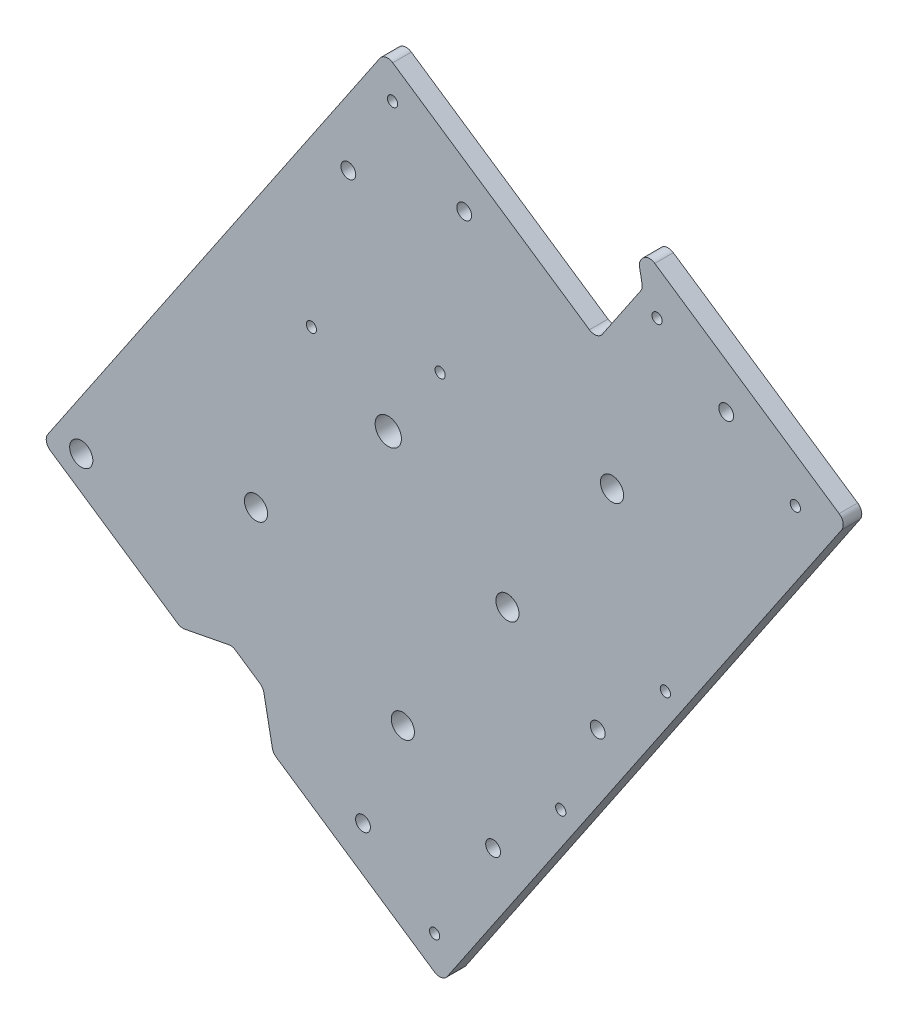
SolidWorks part; units mm, degrees
ref_plane "Front Plane" through (0, 0, 0) normal (0, 0, 1) x (1, 0, 0)
ref_plane "Top Plane" through (0, 0, 0) normal (0, 1, 0) x (1, 0, 0)
ref_plane "Right Plane" through (0, 0, 0) normal (1, 0, 0) x (0, 0, -1)
sketch "Sketch1" plane through (0, 0, 0) normal (0, 0, 1) x (1, 0, 0)
  line L0 (0, 31.75) -> (0, 57.15) construction
  line L1 (31.75, 0) -> (67.31, 0) construction
  line L3 (0, -31.75) -> (0, -97.79) construction
  line L4 (22.4506, -22.4506) -> (58.3717, -58.3717) construction
  line L5 (-22.4506, -22.4506) -> (-72.7401, -72.7401) construction
  line L6 (57.493, 23.8144) -> (29.3332, 12.1502) construction
  line L7 (-40.4112, 40.4112) -> (-22.4506, 22.4506) construction
  line L8 (42.2072, 42.2072) -> (22.4506, 22.4506) construction
  line L9 (71.5729, -29.6465) -> (29.3332, -12.1502) construction
  line L10 (33.5345, -80.9596) -> (12.1502, -29.3332) construction
  line L11 (-37.4226, -90.3462) -> (-12.1502, -29.3332) construction
  circle A0 centre (0, 0) radius 31.75 construction
  circle A3 centre (0, 0) radius 50.8 construction
  dimension "D4" = 63.5
  dimension "D24" = 101.6
  dimension "D2" = 25.4
  dimension "D3" = 35.56
  dimension "D5" = 66.04
  dimension "D6" = 45
  dimension "D7" = 50.8
  dimension "D8" = 71.12
  dimension "D9" = 45
  dimension "D10" = 45
  dimension "D11" = 27.94
  dimension "D12" = 45
  dimension "D13" = 22.5
  dimension "D14" = 22.5
  dimension "D15" = 22.5
  dimension "D16" = 25.4
  dimension "D17" = 45.72
  dimension "D18" = 55.88
  dimension "D19" = 66.04
  dimension "D20" = 22.5
  dimension "D21" = 30.48
sketch "Sketch6" plane through (0, 0, 0) normal (0, 0, 1) x (1, 0, 0)
  line L0 (0, 0) -> (0, 57.15) construction
  line L1 (-68.0069, -76.6709) -> (-109.4868, -48.6565)
  line L2 (-109.4868, -48.6565) -> (-73.9468, 3.9663) construction
  line L3 (-73.9468, 3.9663) -> (-56.6244, -7.7327)
  line L4 (-73.9468, 3.9663) -> (-1.0899, 111.8431)
  line L5 (-1.0899, 111.8431) -> (135.7295, 19.4391)
  line L6 (135.7295, 19.4391) -> (18.4476, -154.2162)
  line L7 (18.4476, -154.2162) -> (-118.3718, -61.8122)
  line L8 (-118.3718, -61.8122) -> (-109.4868, -48.6565)
  arc A0 (0, 57.15) -> (-56.6244, -7.7327) centre (0, 0) ccw
  arc A1 (0, 57.15) -> (70.8293, -29.3385) centre (1.3636, -13.9802) cw
  spline S0 degree 4 poles (72.5802, -14.4204) (72.5732, -14.8939) (72.5509, -15.8408) (72.5026, -17.0238) (72.4142, -18.4418) (72.3202, -19.622) (72.2329, -20.5651) (72.1094, -21.7358) (71.9666, -22.9009) (71.8046, -24.0602) (71.6239, -25.2132) (71.4679, -26.1331) (71.3203, -26.9417) (71.191, -27.6137) (71.0723, -28.2005) (70.9682, -28.6984) (70.8717, -29.1472) (70.8012, -29.4669) (70.7133, -29.8548) (70.619, -30.2629) (70.5011, -30.7621) (70.364, -31.3222) (70.1993, -31.971) (70.0005, -32.7239) (69.7951, -33.4698) (69.582, -34.2143) (69.3614, -34.9567) (69.1333, -35.6968) (68.8388, -36.6189) (68.4706, -37.7207) (68.0195, -38.9988) (67.4748, -40.4488) (66.9013, -41.8877) (66.2993, -43.3149) (65.6691, -44.7298) (65.0111, -46.132) (64.3256, -47.521) (63.613, -48.8963) (62.8736, -50.2574) (62.1078, -51.6038) (61.3159, -52.935) (60.4985, -54.2507) (59.6557, -55.5503) (58.5712, -57.1543) (57.221, -59.0453) (55.576, -61.2004) (53.604, -63.5903) (51.5433, -65.9041) (49.3973, -68.139) (47.1695, -70.2924) (44.8635, -72.3618) (42.4828, -74.3448) (40.0312, -76.2394) (36.8825, -78.4946) (32.9768, -81.016) (28.2508, -83.6809) (21.4155, -86.9191) (14.3083, -89.5267) (6.997, -91.4882) (-0.4519, -92.7974) (-6.6169, -93.4564) (-12.812, -93.702) (-19.0096, -93.5373) (-25.1831, -92.9667) (-31.3064, -91.9964) (-36.5985, -90.8043) (-41.0725, -89.5432) (-44.7523, -88.3359) (-47.6642, -87.2776) (-50.5413, -86.1284) (-53.3811, -84.8896) (-56.1809, -83.563) (-58.5935, -82.3267) (-60.6334, -81.2142) (-62.3138, -80.2525) (-63.6461, -79.4625) (-64.9661, -78.6522) (-66.2736, -77.8217) (-67.4063, -77.0777) (-68.3692, -76.4276) (-69.1659, -75.8779) (-69.7996, -75.4335) (-70.4313, -74.9832) (-71.06, -74.5278) (-71.6725, -74.0775) (-72.2987, -73.6093) (-72.9683, -73.0996) (-73.347, -72.808) (-73.9663, -72.325) (-74.6801, -71.7609) (-75.4046, -71.175) (-76.2838, -70.4507) (-77.1319, -69.735) (-77.9818, -69.0025) (-78.8195, -68.2643) (-79.6511, -67.5155) (-80.4737, -66.7585) (-81.4921, -65.8008) (-82.6974, -64.6343) (-83.8818, -63.4463) (-85.0447, -62.2374) (-85.8084, -61.4205) (-86.1873, -61.0093) (-86.376, -60.8031) knots 0 0 0 0 0 0.008941 0.017882 0.022352 0.026823 0.031293 0.035764 0.044578 0.048985 0.053392 0.057799 0.062207 0.06441 0.066614 0.068817 0.071021 0.072848 0.074676 0.076504 0.078332 0.081987 0.085642 0.089298 0.092953 0.096609 0.100264 0.103919 0.107575 0.114886 0.122197 0.129507 0.136818 0.144129 0.15144 0.158751 0.166062 0.173372 0.180683 0.187994 0.195305 0.202616 0.209927 0.217237 0.231859 0.246481 0.261102 0.275724 0.290346 0.304967 0.319589 0.334211 0.348832 0.363454 0.392697 0.421941 0.451184 0.506141 0.535384 0.564627 0.593871 0.623114 0.652357 0.681601 0.710844 0.740087 0.754709 0.769331 0.783952 0.798574 0.813196 0.827817 0.842439 0.84975 0.857061 0.864371 0.871682 0.878993 0.886304 0.889959 0.893615 0.89727 0.900926 0.904581 0.908237 0.911892 0.915547 0.918186 0.920826 0.926104 0.931382 0.936661 0.941939 0.947217 0.952495 0.957774 0.963052 0.96833 0.978887 0.989443 0.994722 1 1 1 1 1 construction
  spline S1 degree 4 poles (70.8293, -29.3385) (70.8117, -29.4183) (70.776, -29.5781) (70.7133, -29.8548) (70.619, -30.2629) (70.5011, -30.7621) (70.364, -31.3222) (70.1993, -31.971) (70.0005, -32.7239) (69.7951, -33.4698) (69.582, -34.2143) (69.3614, -34.9567) (69.1333, -35.6968) (68.8388, -36.6189) (68.4706, -37.7207) (68.0195, -38.9988) (67.4748, -40.4488) (66.9013, -41.8877) (66.2993, -43.3149) (65.6691, -44.7298) (65.0111, -46.132) (64.3256, -47.521) (63.613, -48.8963) (62.8736, -50.2574) (62.1078, -51.6038) (61.3159, -52.935) (60.4985, -54.2507) (59.6557, -55.5503) (58.5712, -57.1543) (57.221, -59.0453) (55.576, -61.2004) (53.604, -63.5903) (51.5433, -65.9041) (49.3973, -68.139) (47.1695, -70.2924) (44.8635, -72.3618) (42.4828, -74.3448) (40.0312, -76.2394) (36.8825, -78.4946) (32.9768, -81.016) (28.2508, -83.6809) (21.4155, -86.9191) (14.3083, -89.5267) (6.997, -91.4882) (-0.4519, -92.7974) (-6.6169, -93.4564) (-12.812, -93.702) (-19.0096, -93.5373) (-25.1831, -92.9667) (-31.3064, -91.9964) (-36.5985, -90.8043) (-41.0725, -89.5432) (-44.7523, -88.3359) (-47.6642, -87.2776) (-50.5413, -86.1284) (-53.3811, -84.8896) (-56.1809, -83.563) (-58.5935, -82.3267) (-60.6334, -81.2142) (-62.3138, -80.2525) (-63.6461, -79.4625) (-64.9661, -78.6522) (-66.2224, -77.8543) (-67.143, -77.2506) (-67.7363, -76.8537) (-68.0069, -76.6709) knots 0.071021 0.071021 0.071021 0.071021 0.071021 0.072848 0.074676 0.076504 0.078332 0.081987 0.085642 0.089298 0.092953 0.096609 0.100264 0.103919 0.107575 0.114886 0.122197 0.129507 0.136818 0.144129 0.15144 0.158751 0.166062 0.173372 0.180683 0.187994 0.195305 0.202616 0.209927 0.217237 0.231859 0.246481 0.261102 0.275724 0.290346 0.304967 0.319589 0.334211 0.348832 0.363454 0.392697 0.421941 0.451184 0.506141 0.535384 0.564627 0.593871 0.623114 0.652357 0.681601 0.710844 0.740087 0.754709 0.769331 0.783952 0.798574 0.813196 0.827817 0.842439 0.84975 0.857061 0.864371 0.871682 0.878993 0.885158 0.885158 0.885158 0.885158 0.885158
  dimension "D1" = 57.15
  dimension "D2" = 101.6
  dimension "D3" = 63.5
  dimension "D4" = 63.5
  dimension "D5" = 15.875
  dimension "D6" = 101.6
  dimension "D7" = 209.55
extrude "Boss-Extrude2" add sketch "Sketch6" along normal blind 6.35
sketch "Sketch8" plane through (0, 0, 6.35) normal (0, 0, 1) x (1, 0, 0)
  line L0 (-71.0112, -93.7982) -> (-53.3787, -90.3816)
  line L1 (-118.3718, -61.8122) -> (18.4476, -154.2162) construction
  line L2 (-53.3787, -90.3816) -> (-42.8541, -97.4896)
  line L3 (-42.8541, -97.4896) -> (-39.4375, -115.1222)
  line L4 (-39.4375, -115.1222) -> (-71.0112, -93.7982)
  line L5 (18.4476, -154.2162) -> (135.7295, 19.4391) construction
  dimension "D1" = 82.55
  dimension "D2" = 12.7
  dimension "D3" = 12.7
  dimension "D4" = 45
  dimension "D5" = 45
extrude "Cut-Extrude1" cut sketch "Sketch8" against normal through all
sketch "Sketch9" plane through (0, 0, 6.35) normal (0, 0, 1) x (1, 0, 0)
  line L0 (-1.0899, 111.8431) -> (-109.4868, -48.6565)
  line L1 (-1.0899, 111.8431) -> (135.7295, 19.4391)
  line L2 (-109.4868, -48.6565) -> (27.3325, -141.0605)
  line L3 (135.7295, 19.4391) -> (27.3325, -141.0605)
  line L4 (18.4476, -154.2162) -> (135.7295, 19.4391) construction
extrude "Boss-Extrude3" add sketch "Sketch9" against normal through all
sketch "Sketch10" plane through (0, 0, 6.35) normal (0, 0, 1) x (1, 0, 0)
  line L0 (76.6361, 21.2777) -> (4.9965, -84.7966) construction
  line L2 (-39.4375, -115.1222) -> (18.4476, -154.2162) construction
  line L3 (0, 0) -> (-45.2952, -45.2145) construction
  line L4 (-45.2952, -45.2145) -> (4.9965, -84.7966) construction
  line L5 (18.4476, -154.2162) -> (135.7295, 19.4391) construction
  circle A0 centre (4.9965, -84.7966) radius 3.9688
  circle A1 centre (40.8163, -31.7595) radius 3.9687
  circle A2 centre (76.6361, 21.2777) radius 3.9687
  circle A3 centre (-45.2952, -45.2145) radius 3.9687
  dimension "D1" = 7.9375
  dimension "D2" = 50
  dimension "D3" = 50
  dimension "D4" = 128
  dimension "D5" = 64
extrude "Cut-Extrude2" cut sketch "Sketch10" against normal through all
sketch "Sketch11" plane through (0, 0, 6.35) normal (0, 0, 1) x (1, 0, 0)
  circle A0 centre (0, 0) radius 4.5
  dimension "D1" = 9
extrude "Cut-Extrude4" cut sketch "Sketch11" against normal through all contours A0
sketch "Sketch12" plane through (0, 0, 6.35) normal (0, 0, 1) x (1, 0, 0)
  line L0 (135.7295, 19.4391) -> (67.3198, 65.6411)
  line L1 (135.7295, 19.4391) -> (157.0534, 51.0128)
  line L2 (67.3198, 65.6411) -> (88.6438, 97.2148)
  line L3 (157.0534, 51.0128) -> (88.6438, 97.2148)
  line L4 (135.7295, 19.4391) -> (-1.0899, 111.8431) construction
  dimension "D1" = 82.55
  dimension "D2" = 38.1
extrude "Boss-Extrude4" add sketch "Sketch12" against normal through all
sketch "Sketch13" plane through (0, 0, 6.35) normal (0, 0, 1) x (1, 0, 0)
  line L0 (40.8163, -31.7595) -> (76.6361, 21.2777) construction
  line L1 (18.4476, -154.2162) -> (157.0534, 51.0128) construction
  line L2 (58.7262, -5.2409) -> (94.8992, -29.6711) construction
  circle A0 centre (94.8992, -29.6711) radius 1.75
  dimension "D1" = 3.5
  dimension "D2" = 6.35
extrude "Cut-Extrude5" cut sketch "Sketch13" against normal through all
pattern_linear "LPattern1" count 2 spacing 64 along (-0.5597, -0.8287, 0) of "Cut-Extrude5"
sketch "Sketch14" plane through (0, 0, 6.35) normal (0, 0, 1) x (1, 0, 0)
  line L0 (59.0794, -82.7083) -> (94.8992, -29.6711) construction
  line L1 (76.9893, -56.1897) -> (71.727, -52.6357) construction
  line L2 (18.4476, -154.2162) -> (157.0534, 51.0128) construction
  line L3 (115.7406, 63.5892) -> (122.8486, 74.1138) construction
  line L4 (157.0534, 51.0128) -> (88.6438, 97.2148) construction
  circle A0 centre (71.727, -52.6357) radius 2.54
  circle A1 centre (35.9072, -105.6729) radius 2.54
  circle A2 centre (115.7406, 63.5892) radius 2.54
  dimension "D1" = 5.08
  dimension "D2" = 12.7
  dimension "D4" = 12.7
  dimension "D3" = 2
extrude "Cut-Extrude6" cut sketch "Sketch14" against normal through all
sketch "Sketch15" plane through (0, 0, 6.35) normal (0, 0, 1) x (1, 0, 0)
  line L0 (-118.3718, -61.8122) -> (-71.0112, -93.7982) construction
  line L1 (-39.4375, -115.1222) -> (18.4476, -154.2162) construction
  line L2 (18.4476, -154.2162) -> (157.0534, 51.0128) construction
  line L3 (-1.0899, 111.8431) -> (-118.3718, -61.8122) construction
  line L4 (67.3198, 65.6411) -> (-1.0899, 111.8431) construction
  circle A0 centre (-105.1473, -59.2498) radius 1.75
  circle A1 centre (15.8851, -140.9917) radius 1.75
  circle A2 centre (59.0794, -82.7083) radius 1.75 construction
  circle A3 centre (1.4726, 98.6186) radius 1.75
  dimension "D1" = 9.525
  dimension "D2" = 9.525
  dimension "D3" = 9.525
  dimension "D4" = 9.525
  dimension "D5" = 9.525
  dimension "D6" = 9.525
extrude "Cut-Extrude7" cut sketch "Sketch15" against normal through all
sketch "Sketch16" plane through (0, 0, 6.35) normal (0, 0, 1) x (1, 0, 0)
  line L0 (157.0534, 51.0128) -> (88.6438, 97.2148) construction
  line L1 (88.6438, 97.2148) -> (67.3198, 65.6411) construction
  line L2 (18.4476, -154.2162) -> (157.0534, 51.0128) construction
  circle A0 centre (92.0604, 79.5822) radius 1.75
  circle A1 centre (139.4209, 47.5962) radius 1.75
  circle A2 centre (94.8992, -29.6711) radius 1.75 construction
  dimension "D1" = 12.7
  dimension "D2" = 12.7
  dimension "D3" = 12.7
  dimension "D4" = 12.7
extrude "Cut-Extrude8" cut sketch "Sketch16" against normal through all
sketch "Sketch17" plane through (0, 0, 6.35) normal (0, 0, 1) x (1, 0, 0)
  line L0 (0, 0) -> (-26.3114, 17.77) construction
  line L1 (0, 0) -> (17.77, 26.3114) construction
  line L2 (18.4476, -154.2162) -> (157.0534, 51.0128) construction
  circle A0 centre (-26.3114, 17.77) radius 1.75
  circle A1 centre (17.77, 26.3114) radius 1.75
  circle A2 centre (94.8992, -29.6711) radius 1.75 construction
  dimension "D1" = 31.75
extrude "Cut-Extrude9" cut sketch "Sketch17" against normal through all
sketch "Sketch19" plane through (0, 0, 6.35) normal (0, 0, 1) x (1, 0, 0)
  line L0 (88.6438, 97.2148) -> (67.3198, 65.6411) construction
  line L1 (67.3198, 65.6411) -> (-1.0899, 111.8431) construction
  line L2 (18.4476, -154.2162) -> (-118.3718, -61.8122) construction
  line L3 (-65.6802, -85.9048) -> (35.6087, 64.0702) construction
  line L4 (-73.9468, 3.9663) -> (-1.0899, 111.8431) construction
  circle A0 centre (35.6087, 64.0702) radius 3.9687 construction
  circle A1 centre (-65.6802, -85.9048) radius 3.9687
  dimension "D1" = 7.9375
  dimension "D2" = 25.4
  dimension "D3" = 19.05
  dimension "D4" = 9.525
extrude "Cut-Extrude11" cut sketch "Sketch19" against normal through all
sketch "Sketch21" plane through (0, 0, 6.35) normal (0, 0, 1) x (1, 0, 0)
  line L0 (-73.9468, 3.9663) -> (-1.0899, 111.8431) construction
  line L1 (67.3198, 65.6411) -> (-1.0899, 111.8431) construction
  line L2 (-118.3718, -61.8122) -> (-71.0112, -93.7982) construction
  line L3 (-39.4375, -115.1222) -> (18.4476, -154.2162) construction
  line L5 (-8.6493, -120.5906) -> (115.7406, 63.5892) construction
  line L6 (18.4476, -154.2162) -> (157.0534, 51.0128) construction
  line L7 (-118.3718, -61.8122) -> (-109.4868, -48.6565) construction
  circle A0 centre (-13.6663, 70.5302) radius 2.54
  circle A1 centre (26.007, 78.2175) radius 2.54
  circle A2 centre (-86.7294, -71.6888) radius 2.54
  circle A3 centre (-8.6493, -120.5906) radius 2.54
  circle A4 centre (35.9072, -105.6729) radius 2.54 construction
  dimension "D1" = 12.7
  dimension "D2" = 12.7
  dimension "D3" = 9.525
  dimension "D4" = 12.7
  dimension "D5" = 41.275
  dimension "D6" = 31.75
  dimension "D7" = 41.275
extrude "Cut-Extrude12" cut sketch "Sketch21" against normal through all
sketch "Sketch22" plane through (0, 0, 6.35) normal (0, 0, 1) x (1, 0, 0)
  circle A0 centre (-105.1473, -59.2498) radius 3.9688
  dimension "D1" = 7.9375
extrude "Cut-Extrude13" cut sketch "Sketch22" against normal through all
sketch "Sketch23" plane through (0, 0, 6.35) normal (0, 0, 1) x (1, 0, 0)
  circle A0 centre (-86.7294, -71.6888) radius 4.8851
  circle A1 centre (-65.6802, -85.9048) radius 5.6704
extrude "Boss-Extrude5" add sketch "Sketch23" against normal through all
sketch "Sketch24" plane through (0, 0, 6.35) normal (0, 0, 1) x (1, 0, 0)
  line L0 (85.8006, 93.0049) -> (87.1672, 85.9519)
  line L1 (88.6438, 97.2148) -> (67.3198, 65.6411) construction
  line L2 (87.1672, 85.9519) -> (71.5296, 62.7979)
  line L3 (71.5296, 62.7979) -> (67.3198, 65.6411)
  line L4 (67.3198, 65.6411) -> (85.8006, 93.0049)
  line L5 (67.3198, 65.6411) -> (-1.0899, 111.8431) construction
  dimension "D1" = 45
  dimension "D4" = 5.08
  dimension "D5" = 5.08
extrude "Cut-Extrude14" cut sketch "Sketch24" against normal through all
fillet "Fillet1" radius 3.175 12 edges at (18.4476, -154.2162, 3.175) (-39.4375, -115.1222, 3.175) (-42.8541, -97.4896, 3.175) (-53.3787, -90.3816, 3.175) (-71.0112, -93.7982, 3.175) (-118.3718, -61.8122, 3.175) (157.0534, 51.0128, 3.175) (-1.0899, 111.8431, 3.175) (71.5296, 62.7979, 3.175) (85.8006, 93.0049, 3.175) (87.1672, 85.9519, 3.175) (88.6438, 97.2148, 3.175)
